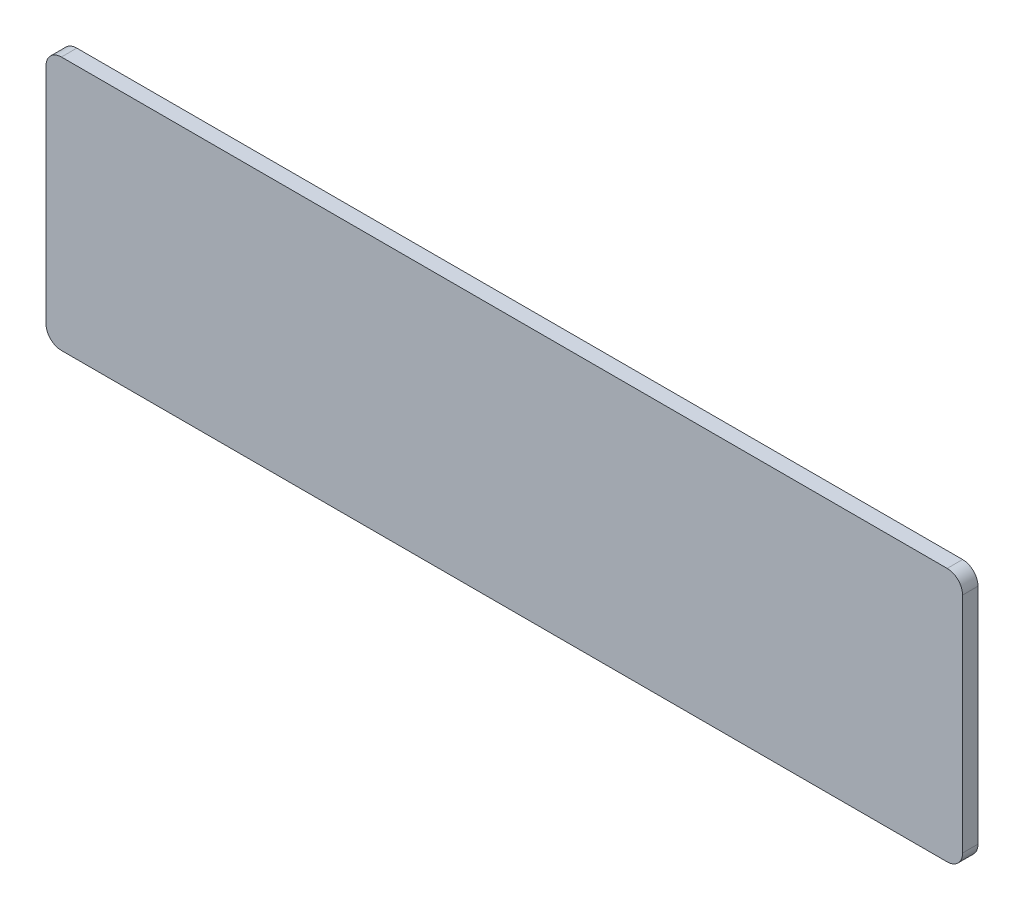
SolidWorks part; units mm, degrees
ref_plane "Płaszczyzna przednia" through (0, 0, 0) normal (0, 0, 1) x (1, 0, 0)
ref_plane "Płaszczyzna górna" through (0, 0, 0) normal (0, 1, 0) x (1, 0, 0)
ref_plane "Płaszczyzna prawa" through (0, 0, 0) normal (1, 0, 0) x (0, 0, -1)
sketch "Szkic1" plane through (0, 0, 0) normal (0, 0, 1) x (1, 0, 0)
  line L0 (-57.5, -16.5) -> (57.5, -16.5) construction
  line L1 (-59.5, 14.5) -> (-59.5, -14.5) construction
  line L2 (57.5, 16.5) -> (-57.5, 16.5) construction
  line L3 (59.5, -14.5) -> (59.5, 14.5) construction
  line L4 (-57.5, -16.5) -> (57.5, -16.5)
  line L5 (-59.5, 14.5) -> (-59.5, -14.5)
  line L6 (57.5, 16.5) -> (-57.5, 16.5)
  line L7 (59.5, -14.5) -> (59.5, 14.5)
  arc A4 (57.5, -16.5) -> (59.5, -14.5) centre (57.5, -14.5) ccw
  arc A5 (-59.5, -14.5) -> (-57.5, -16.5) centre (-57.5, -14.5) ccw
  arc A6 (-57.5, 16.5) -> (-59.5, 14.5) centre (-57.5, 14.5) ccw
  arc A7 (59.5, 14.5) -> (57.5, 16.5) centre (57.5, 14.5) ccw
extrude "Dodanie-wyciągnięcie1" add sketch "Szkic1" along normal blind 2
sketch "Szkic4" plane through (0, 0, 0) normal (0, 0, -1) x (-1, 0, 0)
  line L0 (55.5, -12.5) -> (-55.5, -12.5) construction
  line L1 (53, -12) -> (-53, -12)
  line L2 (55, -10) -> (55, 10)
  line L3 (53, 12) -> (-53, 12)
  line L4 (-55, -10) -> (-55, 10)
  line L5 (-55.5, 12.5) -> (55.5, 12.5) construction
  line L7 (55.5, 12.5) -> (55.5, -12.5) construction
  line L9 (-55.5, -12.5) -> (-55.5, 12.5) construction
  arc A0 (-53, 12) -> (-55, 10) centre (-53, 10) ccw
  arc A1 (-53, -12) -> (-55, -10) centre (-53, -10) cw
  arc A2 (55, 10) -> (53, 12) centre (53, 10) ccw
  arc A3 (53, -12) -> (55, -10) centre (53, -10) ccw
  dimension "D5" = 2
  dimension "D1" = 0.5
  dimension "D2" = 0.5
  dimension "D3" = 0.5
  dimension "D4" = 0.5
extrude "Dodanie-wyciągnięcie2" add sketch "Szkic4" along normal blind 1
